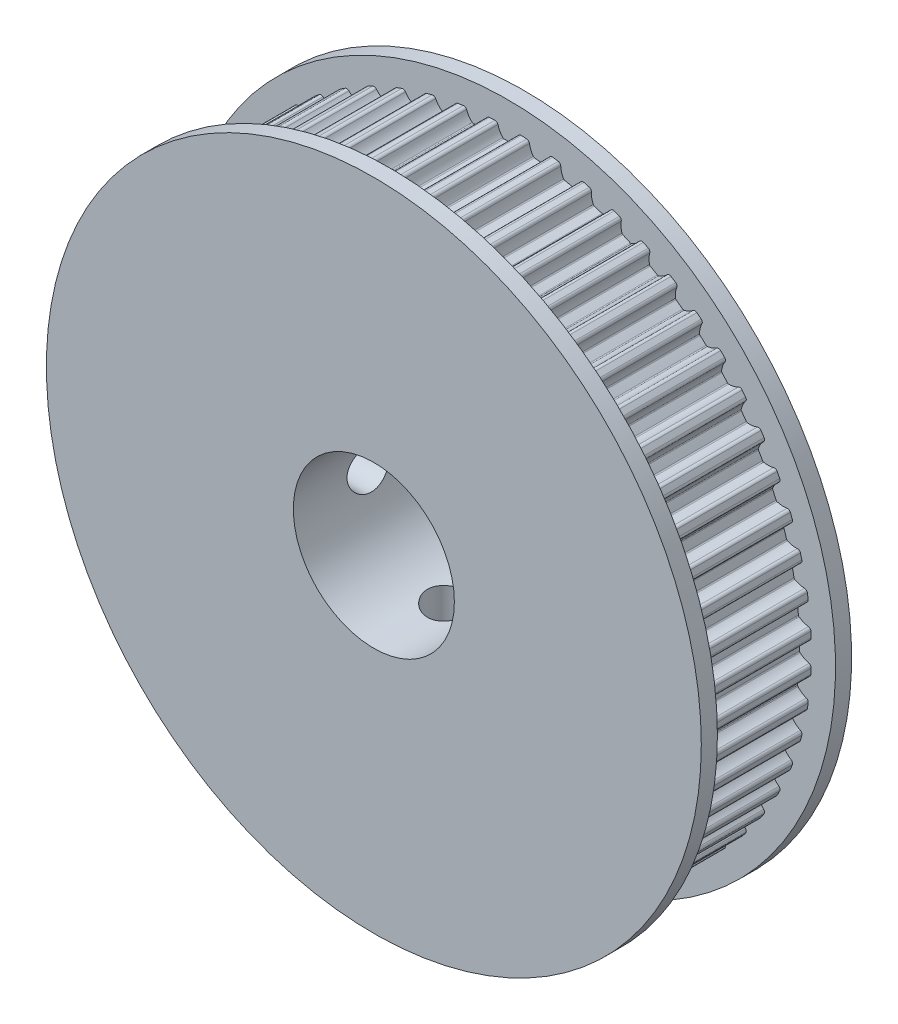
SolidWorks part; units mm, degrees
material "6061-T6 (SS)"
ref_plane "前基準面" through (0, 0, 0) normal (0, 0, 1) x (1, 0, 0)
ref_plane "上基準面" through (0, 0, 0) normal (0, 1, 0) x (1, 0, 0)
ref_plane "右基準面" through (0, 0, 0) normal (1, 0, 0) x (0, 0, -1)
sketch "草圖1" plane through (0, 0, 0) normal (0, 0, 1) x (1, 0, 0)
  circle A0 centre (0, 0) radius 28.265
  dimension "D1" = 56.53
extrude "填料-伸長1" add sketch "草圖1" along normal mid plane 11
sketch "草圖2" plane through (0, 0, 5.5) normal (0, 0, 1) x (1, 0, 0)
  line L0 (0, 0) -> (0, 28.265) construction
  line L1 (0, 28.265) -> (0, 28.519) construction
  line L2 (-0.975, 28.519) -> (0.975, 28.519) construction
  circle A0 centre (0, 0) radius 28.265 construction
  arc A1 (-0.3831, 27.1523) -> (0.3831, 27.1523) centre (0, 0) cw
  arc A2 (-0.3831, 27.1523) -> (-0.497, 27.2023) centre (-0.3852, 27.3023) cw
  arc A3 (-0.497, 27.2023) -> (-0.9381, 28.0284) centre (0.975, 28.519) cw
  arc A4 (-1.2214, 28.2386) -> (-0.9381, 28.0284) centre (-1.2093, 27.9589) cw
  arc A5 (0.3831, 27.1523) -> (0.497, 27.2023) centre (0.3852, 27.3023) ccw
  arc A6 (0.497, 27.2023) -> (0.9381, 28.0284) centre (-0.975, 28.519) ccw
  arc A7 (1.2214, 28.2386) -> (0.9381, 28.0284) centre (1.2093, 27.9589) ccw
  arc A8 (-1.2214, 28.2386) -> (1.2214, 28.2386) centre (0, 0) cw
  dimension "D1" = 0.15
  dimension "D2" = 1.975
  dimension "D3" = 0.28
  dimension "D4" = 1.11
  dimension "D5" = 0.254
  dimension "D6" = 1.95
extrude "除料-伸長1" cut sketch "草圖2" against normal through all and the other way through all
pattern_circular "環狀複製排列1" count 60 over 360 about axis through (0, 0, 0) along (0, 0, 1) of "除料-伸長1"
sketch "草圖3" plane through (0, 0, 5.5) normal (0, 0, 1) x (1, 0, 0)
  circle A0 centre (0, 0) radius 30.5
  dimension "D1" = 61
extrude "填料-伸長2" add sketch "草圖3" along normal blind 1.5
sketch "草圖9" plane through (0, 0, -5.5) normal (0, 0, -1) x (-1, 0, 0)
  circle A0 centre (0, 0) radius 30.5
  circle A1 centre (0, 0) radius 30.5 construction
extrude "填料-伸長3" add sketch "草圖9" along normal blind 1.5
sketch "草圖4" plane through (0, 0, 7) normal (0, 0, 1) x (1, 0, 0)
  circle A0 centre (0, 0) radius 7.5
  dimension "D1" = 15
extrude "除料-伸長2" cut sketch "草圖4" against normal through all
sketch "草圖10" plane through (0, 0, 0) normal (0, 1, 0) x (1, 0, 0)
  circle A0 centre (0, 0) radius 2
  dimension "D1" = 4
extrude "除料-伸長3" cut sketch "草圖10" against normal through all
sketch "草圖11" plane through (0, 0, 0) normal (1, 0, 0) x (0, 0, -1)
  circle A0 centre (0, 0) radius 2
  dimension "D1" = 4
extrude "除料-伸長4" cut sketch "草圖11" against normal through all
